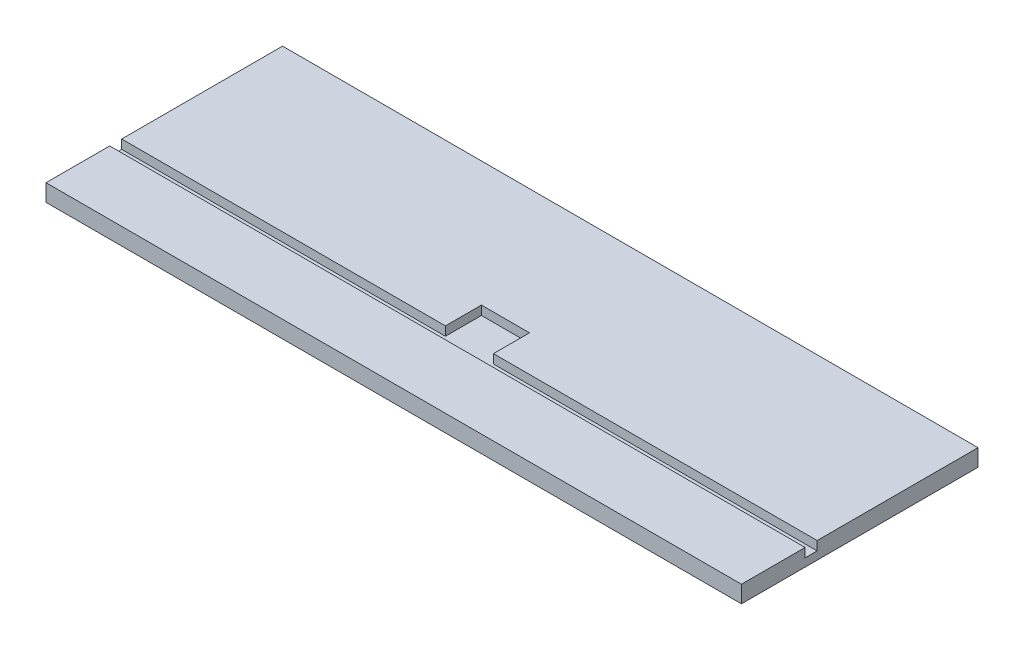
SolidWorks part; units mm, degrees
ref_plane "Front Plane" through (0, 0, 0) normal (0, 0, 1) x (1, 0, 0)
ref_plane "Top Plane" through (0, 0, 0) normal (0, 1, 0) x (1, 0, 0)
ref_plane "Right Plane" through (0, 0, 0) normal (1, 0, 0) x (0, 0, -1)
sketch "Sketch1" plane through (0, 0, 0) normal (0, 1, 0) x (1, 0, 0)
  line L1 (-367.5, -125) -> (367.5, -125)
  line L2 (-367.5, -125) -> (-367.5, 125)
  line L3 (-367.5, 125) -> (367.5, 125)
  line L4 (367.5, -125) -> (367.5, 125)
  line L5 (-367.5, -125) -> (367.5, 125) construction
  line L6 (-367.5, 125) -> (367.5, -125) construction
  point P0 (0, 0)
  dimension "D1" = 735
  dimension "D2" = 250
extrude "Boss-Extrude1" add sketch "Sketch1" along normal blind 18
sketch "Sketch4" plane through (0, 18, 0) normal (0, 1, 0) x (1, 0, 0)
  line L0 (367.5, 125) -> (-367.5, 125) construction
  line L1 (-390.6445, -45) -> (-25.4, -45)
  line L2 (-390.6445, -45) -> (-390.6445, -57.7)
  line L3 (-390.6445, -57.7) -> (418.9302, -57.7)
  line L4 (418.9302, -45) -> (418.9302, -57.7)
  line L5 (-25.4, -45) -> (-25.4, -6.9)
  line L6 (-25.4, -6.9) -> (25.4, -6.9)
  line L7 (25.4, -6.9) -> (25.4, -45)
  line L8 (25.4, -45) -> (418.9302, -45)
  dimension "D1" = 170
  dimension "D2" = 12.7
  dimension "D3" = 25.4
  dimension "D4" = 25.4
  dimension "D5" = 50.8
extrude "Cut-Extrude1" cut sketch "Sketch4" against normal blind 9.525
